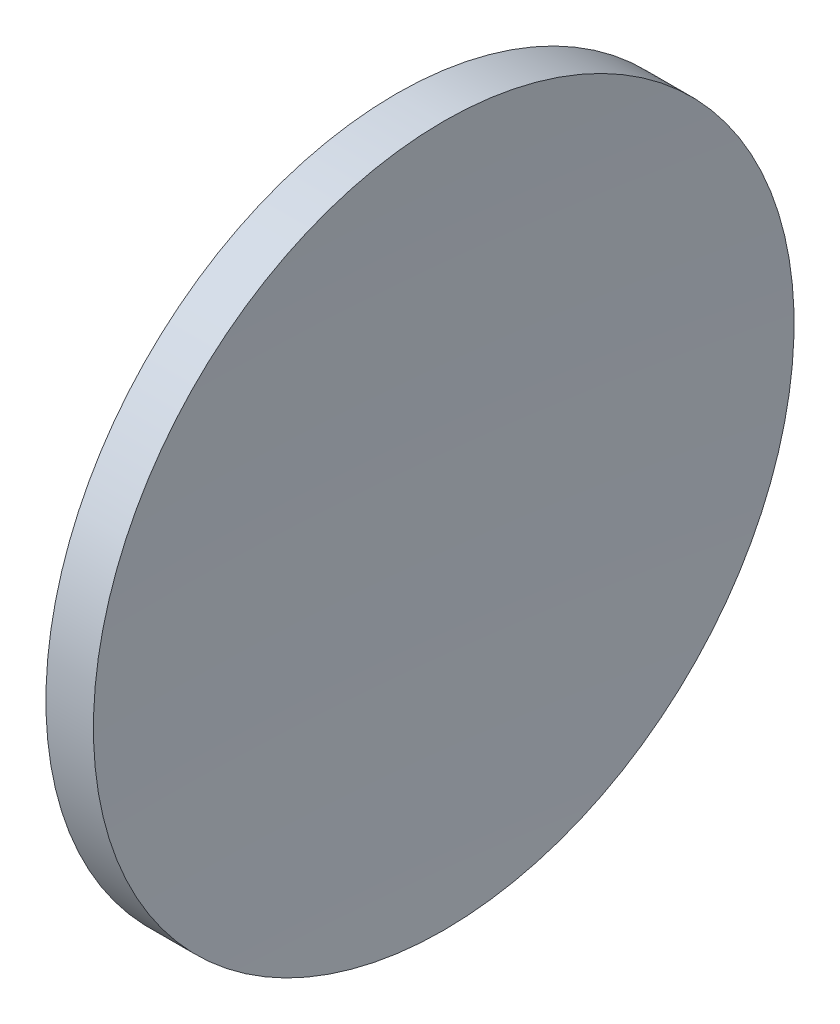
SolidWorks part; units mm, degrees
ref_plane "前视基准面" through (0, 0, 0) normal (0, 0, 1) x (1, 0, 0)
ref_plane "上视基准面" through (0, 0, 0) normal (0, 1, 0) x (1, 0, 0)
ref_plane "右视基准面" through (0, 0, 0) normal (1, 0, 0) x (0, 0, -1)
sketch "草图1" plane through (0, 0, 0) normal (0, 0, 1) x (1, 0, 0)
  line L0 (231.889, 130.4337) -> (271.8964, 130.4337) construction
  line L1 (247.0465, 155.4337) -> (250.4363, 155.4337)
  line L2 (249.7821, 130.4337) -> (245.2821, 130.4337)
  arc A0 (247.0465, 155.4337) -> (245.2821, 130.4337) centre (423.2821, 130.4337) ccw
  arc A1 (250.4363, 155.4337) -> (249.7821, 130.4337) centre (727.7821, 130.4337) ccw
  dimension "D1" = 178
  dimension "D2" = 478
revolve "旋转1" add sketch "草图1" angle 360 about L0
